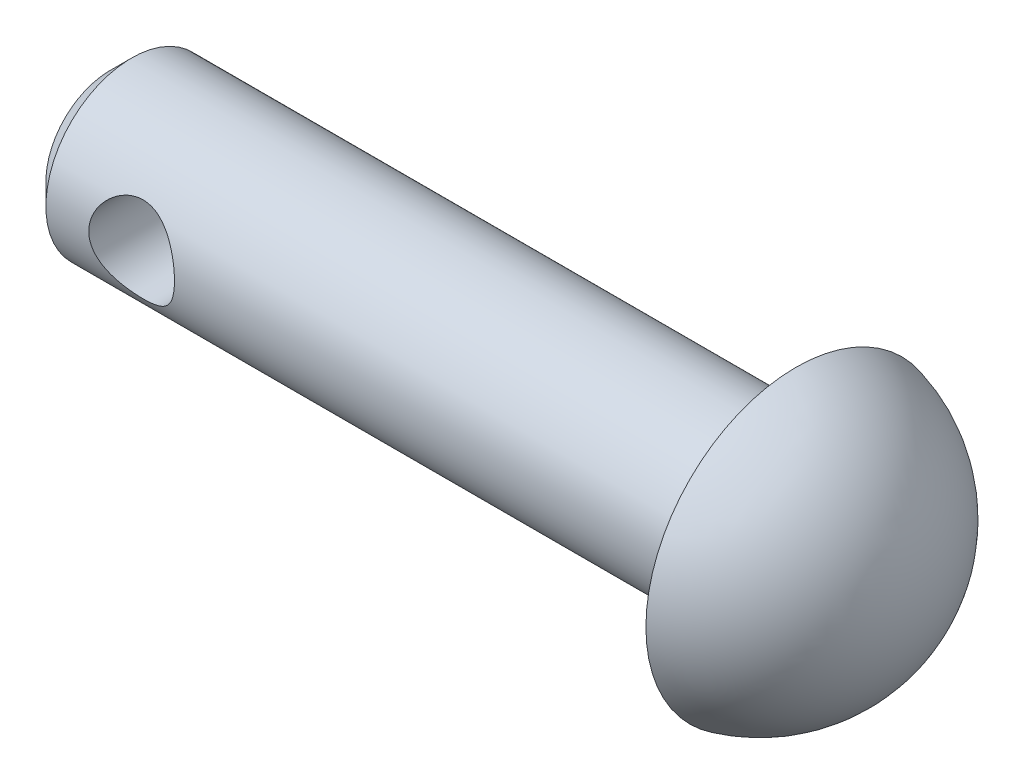
SolidWorks part; units mm, degrees
ref_plane "Front Plane" through (0, 0, 0) normal (0, 0, 1) x (1, 0, 0)
ref_plane "Top Plane" through (0, 0, 0) normal (0, 1, 0) x (1, 0, 0)
ref_plane "Right Plane" through (0, 0, 0) normal (1, 0, 0) x (0, 0, -1)
sketch "Sketch1" plane through (0, 0, 0) normal (1, 0, 0) x (0, 0, -1)
  circle A0 centre (0, 0) radius 2
  dimension "D1" = 4
extrude "Boss-Extrude1" add sketch "Sketch1" against normal blind 16
sketch "Sketch2" plane through (0, 0, 0) normal (0, 0, 1) x (1, 0, 0)
  line L0 (-16, 2) -> (-16, -2) construction
  circle A0 centre (-13.5, 0) radius 1
  dimension "D1" = 2
  dimension "D2" = 2.5
extrude "Cut-Extrude1" cut sketch "Sketch2" against normal through all both and the other way through all
sketch "Sketch3" plane through (0, 0, 0) normal (0, 1, 0) x (1, 0, 0)
  line L0 (-5.0978, 0) -> (5.0691, 0) construction
  line L1 (2.7574, 0) -> (0, 0)
  line L2 (0, 0) -> (0, 3.5)
  arc A0 (0, 3.5) -> (2.7574, 0) centre (-0.8426, 0) cw
  point P7 (0, 0)
  dimension "D2" = 3.6
  dimension "D1" = 3.5
revolve "Revolve1" add sketch "Sketch3" angle 360 about L0
chamfer "Chamfer1" distance 0.5 angle 45 1 edges at (-16, 0, -2)
